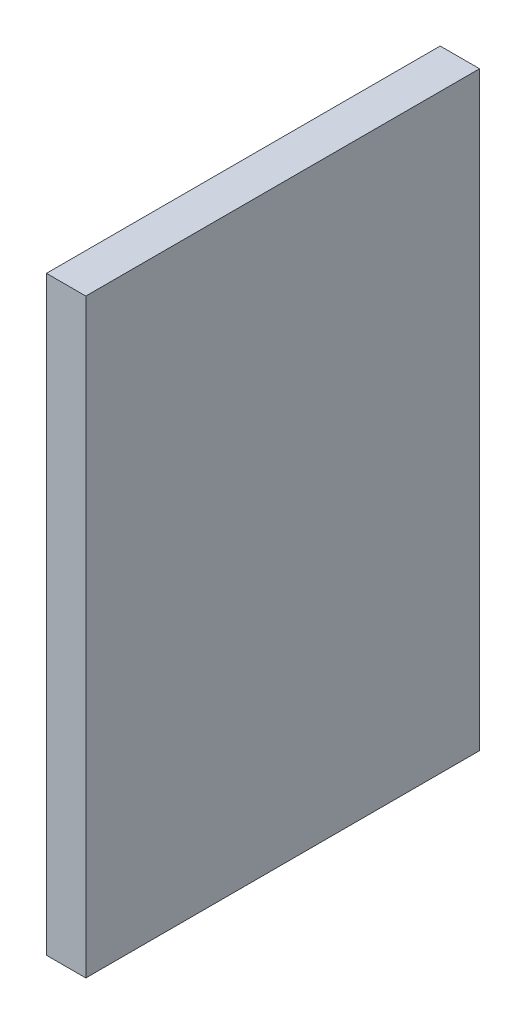
SolidWorks part; units mm, degrees
ref_plane "Front Plane" through (0, 0, 0) normal (0, 0, 1) x (1, 0, 0)
ref_plane "Top Plane" through (0, 0, 0) normal (0, 1, 0) x (1, 0, 0)
ref_plane "Right Plane" through (0, 0, 0) normal (1, 0, 0) x (0, 0, -1)
sketch "Sketch1" plane through (0, 0, 0) normal (1, 0, 0) x (0, 0, -1)
  line L1 (50, -75) -> (-50, -75)
  line L2 (50, -75) -> (50, 75)
  line L3 (50, 75) -> (-50, 75)
  line L4 (-50, -75) -> (-50, 75)
  line L5 (50, -75) -> (-50, 75) construction
  line L6 (50, 75) -> (-50, -75) construction
  point P0 (0, 0)
  dimension "D1" = 150
  dimension "D2" = 100
extrude "Boss-Extrude1" add sketch "Sketch1" along normal blind 10
